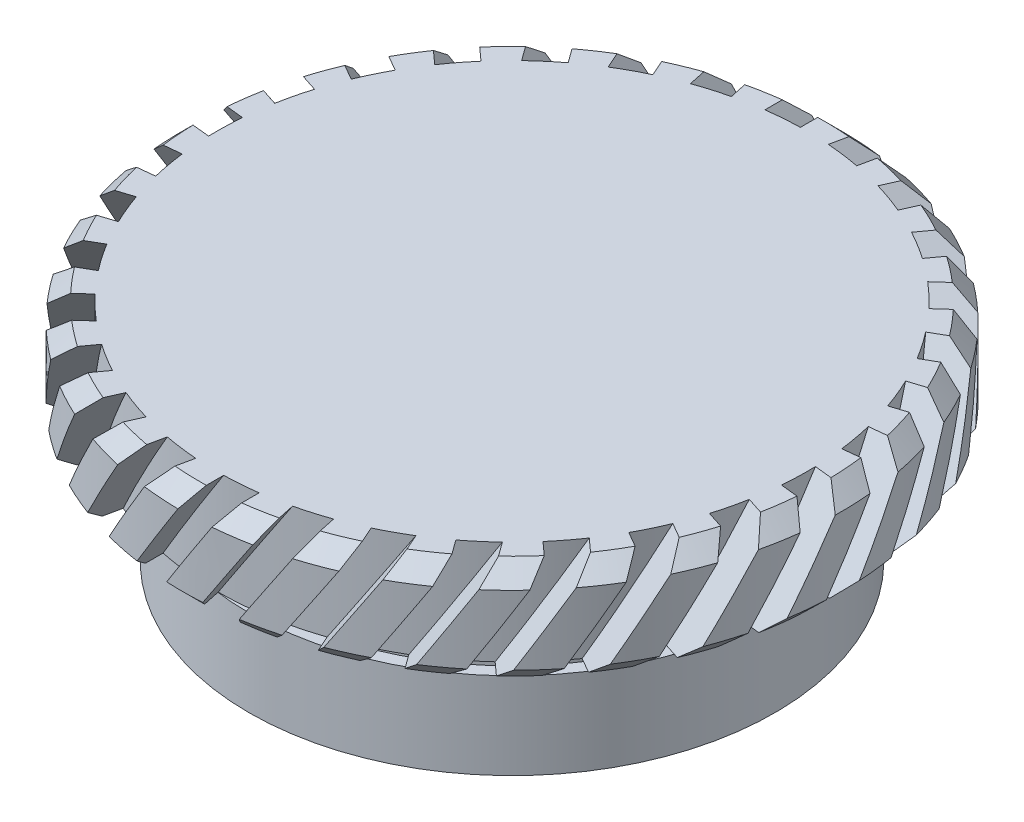
SolidWorks part; units mm, degrees
ref_plane "前视基准面" through (0, 0, 0) normal (0, 0, 1) x (1, 0, 0)
ref_plane "上视基准面" through (0, 0, 0) normal (0, 1, 0) x (1, 0, 0)
ref_plane "右视基准面" through (0, 0, 0) normal (1, 0, 0) x (0, 0, -1)
sketch "草图1" plane through (0, 0, 0) normal (0, 0, 1) x (1, 0, 0)
  line L0 (0, 66.6288) -> (0, -106.6399) construction
  line L1 (-97.6622, 0) -> (93.4292, 0) construction
  line L2 (0, 21.8713) -> (9.525, 21.8713)
  line L3 (9.525, 21.8713) -> (9.525, 18.8713)
  line L4 (7.25, 18.8713) -> (7.25, 17.8713)
  line L5 (7.25, 18.8713) -> (9.525, 18.8713)
  line L6 (7.6, 17.8713) -> (7.6, 15.3713)
  line L7 (7.25, 17.8713) -> (7.6, 17.8713)
  line L8 (6.25, 18.8713) -> (6.25, 15.3713)
  line L9 (0, 21.8713) -> (0, 18.8713)
  line L10 (6.25, 15.3713) -> (7.6, 15.3713)
  line L11 (0, 18.8713) -> (6.25, 18.8713)
  dimension "D1" = 9.525
  dimension "D2" = 3
  dimension "D3" = 7.25
  dimension "D4" = 7.6
  dimension "D5" = 6.25
  dimension "D6" = 1
  dimension "D7" = 2.5
revolve "旋转2" add sketch "草图1" angle 360 about L0
cosmetic thread "装饰螺纹线1" parameters "D2"=15
chamfer "倒角1" distance 0.5 angle 45 2 edges at (0, 21.8713, 9.525) (0, 18.8713, 9.525)
sketch "草图2" plane through (0, 0, 0) normal (0, 0, 1) x (1, 0, 0)
  line L0 (1.1082, 23.3033) -> (-5.3395, 13.2735)
  line L1 (1.1082, 23.3033) -> (1.7811, 22.8706)
  line L2 (-5.3395, 13.2735) -> (-4.6666, 12.8409)
  line L3 (1.7811, 22.8706) -> (-4.6666, 12.8409)
  dimension "D1" = 0.8
surface "曲面-等距1" parameters "D1"=1
extrude "切除-拉伸1" cut sketch "草图2" against normal up to surface (21.5473 mm away) from offset 30
delete or keep bodies "实体-删除/保留 1" type delete bodies bodies 107
pattern_circular "阵列(圆周)2" count 30 over 360 about axis through (0, 0, 0) along (0, 1, 0) of "切除-拉伸1"
